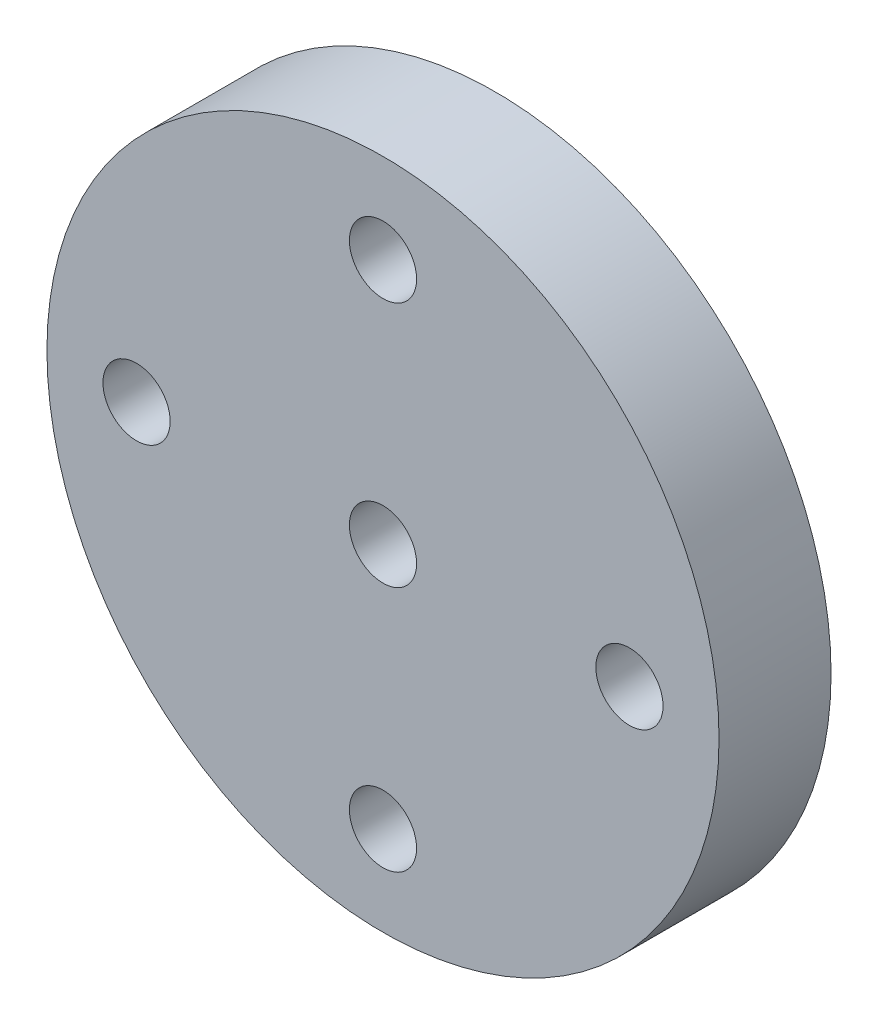
SolidWorks part; units mm, degrees
ref_plane "前视基准面" through (0, 0, 0) normal (0, 0, 1) x (1, 0, 0)
ref_plane "上视基准面" through (0, 0, 0) normal (0, 1, 0) x (1, 0, 0)
ref_plane "右视基准面" through (0, 0, 0) normal (1, 0, 0) x (0, 0, -1)
curve "输入的曲线1"
curve "输入的曲线2"
curve "输入的曲线3"
curve "输入的曲线4"
curve "输入的曲线5"
curve "输入的曲线6"
sketch "草图2" plane through (0, 0, 0) normal (0, 0, 1) x (1, 0, 0)
  circle A0 centre (2507.6401, 4716.0029) radius 1.5
  circle A1 centre (2507.6401, 4705.0029) radius 1.5
  circle A2 centre (2507.6401, 4727.0029) radius 1.5
  circle A3 centre (2496.6401, 4716.0029) radius 1.5
  circle A4 centre (2518.6401, 4716.0029) radius 1.5
  circle A5 centre (2507.6401, 4716.0029) radius 15
extrude "凸台-拉伸1" add sketch "草图2" along normal blind 5
